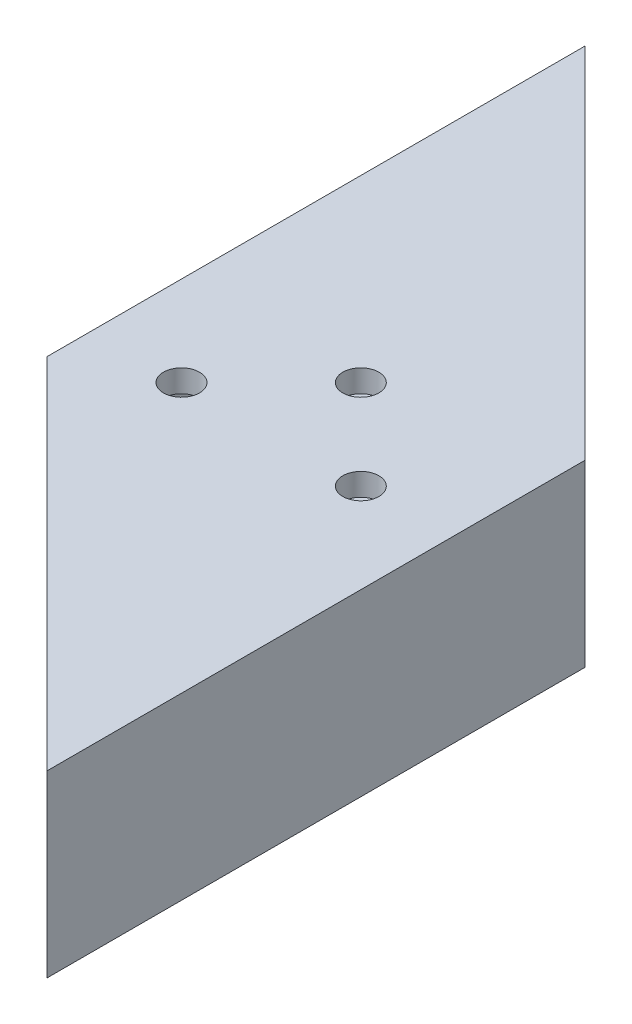
SolidWorks part; units mm, degrees
ref_plane "Front Plane" through (0, 0, 0) normal (0, 0, 1) x (1, 0, 0)
ref_plane "Top Plane" through (0, 0, 0) normal (0, 1, 0) x (1, 0, 0)
ref_plane "Right Plane" through (0, 0, 0) normal (1, 0, 0) x (0, 0, -1)
sketch "Sketch1" plane through (0, 0, 0) normal (0, 0, 1) x (1, 0, 0)
  line L1 (0, 0) -> (50.8, 0)
  line L2 (0, 0) -> (0, 25.4)
  line L3 (0, 25.4) -> (50.8, 25.4)
  line L4 (50.8, 0) -> (50.8, 25.4)
  line L5 (3.175, 3.175) -> (47.625, 3.175)
  line L6 (3.175, 3.175) -> (3.175, 22.225)
  line L7 (3.175, 22.225) -> (47.625, 22.225)
  line L8 (47.625, 3.175) -> (47.625, 22.225)
  dimension "D1" = 25.4
  dimension "D2" = 50.8
  dimension "D3" = 3.175
  dimension "D4" = 3.175
  dimension "D5" = 3.175
  dimension "D6" = 3.175
extrude "Boss-Extrude1" add sketch "Sketch1" along normal blind 127
sketch "Sketch2" plane through (0, 25.4, 0) normal (0, 1, 0) x (1, 0, 0)
  line L0 (0, 0) -> (50.8, -50.8)
  line L1 (50.8, -127) -> (50.8, 0) construction
  line L2 (50.8, -50.8) -> (50.8, 0)
  line L3 (50.8, 0) -> (0, 0)
  line L5 (0, -76.2) -> (0, -127)
  line L6 (0, -127) -> (0, 0) construction
  line L7 (0, -127) -> (50.8, -127)
  line L8 (50.8, -127) -> (0, -76.2)
  dimension "D1" = 45
  dimension "D2" = 45
extrude "Cut-Extrude1" cut sketch "Sketch2" against normal blind 127
sketch "Sketch3" plane through (0, 25.4, 0) normal (0, 1, 0) x (1, 0, 0)
  line L0 (50.8, -50.8) -> (0, -50.8) construction
  line L1 (0, -76.2) -> (0, 0) construction
  line L2 (12.7, -69.85) -> (38.1, -69.85) construction
  line L6 (25.4, -69.85) -> (25.4, -57.15) construction
  circle A0 centre (12.7, -69.85) radius 2.5527
  circle A1 centre (38.1, -69.85) radius 2.5527
  circle A2 centre (25.4, -57.15) radius 2.5527
  point P11 (25.4, -50.8)
  dimension "D3" = 5.1054
  dimension "D1" = 12.7
  dimension "D2" = 25.4
  dimension "D4" = 19.05
extrude "Cut-Extrude2" cut sketch "Sketch3" against normal blind 25.4
